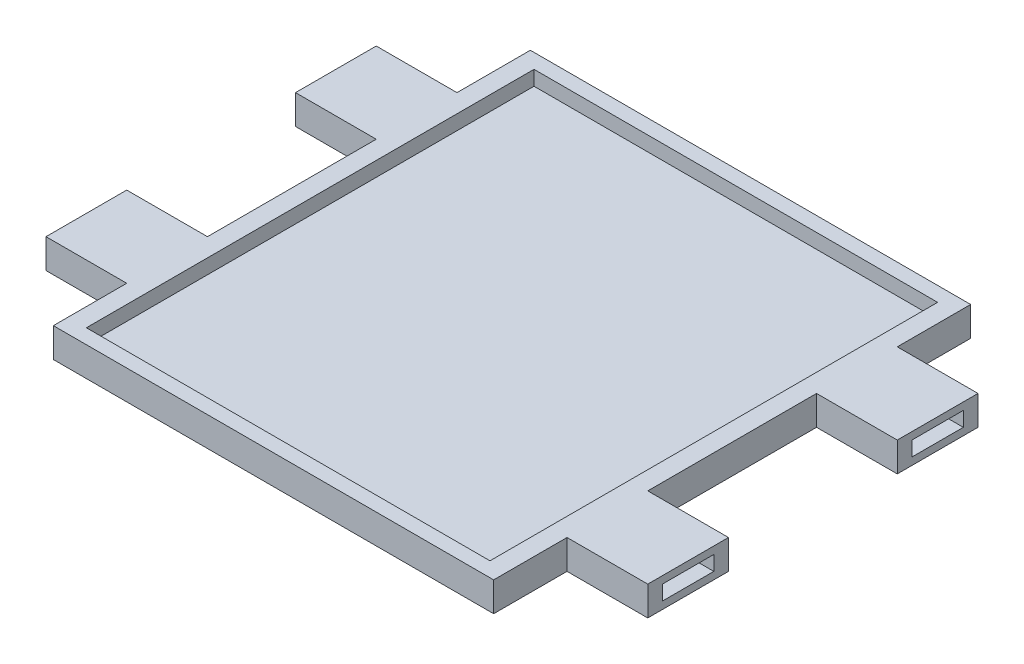
SolidWorks part; units mm, degrees
ref_plane "Alzado" through (0, 0, 0) normal (0, 0, 1) x (1, 0, 0)
ref_plane "Planta" through (0, 0, 0) normal (0, 1, 0) x (1, 0, 0)
ref_plane "Vista lateral" through (0, 0, 0) normal (1, 0, 0) x (0, 0, -1)
sketch "Croquis1" plane through (0, 0, 0) normal (0, 1, 0) x (1, 0, 0)
  line L0 (30, -32.5) -> (30, -22.5)
  line L1 (-30, 32.5) -> (30, 32.5)
  line L2 (30, -22.5) -> (30, -11.5) construction
  line L3 (-30, -32.5) -> (30, -32.5)
  line L4 (30, 11.5) -> (30, 22.5) construction
  line L5 (-30, 32.5) -> (30, -32.5) construction
  line L6 (-30, -32.5) -> (30, 32.5) construction
  line L7 (30, -22.5) -> (41, -22.5)
  line L8 (41, -22.5) -> (41, -11.5)
  line L9 (41, -11.5) -> (30, -11.5)
  line L10 (30, -11.5) -> (30, 11.5)
  line L11 (30, 11.5) -> (41, 11.5)
  line L12 (41, 11.5) -> (41, 22.5)
  line L13 (41, 22.5) -> (30, 22.5)
  line L14 (30, 22.5) -> (30, 32.5)
  line L15 (-30, 32.5) -> (-30, 22.5)
  line L16 (-30, 22.5) -> (-41, 22.5)
  line L17 (-41, 22.5) -> (-41, 11.5)
  line L18 (-41, 11.5) -> (-30, 11.5)
  line L19 (-30, 11.5) -> (-30, -11.5)
  line L20 (-30, -11.5) -> (-41, -11.5)
  line L21 (-41, -11.5) -> (-41, -22.5)
  line L22 (-41, -22.5) -> (-30, -22.5)
  line L23 (-30, -22.5) -> (-30, -32.5)
  line L24 (-30, 11.5) -> (-30, 22.5) construction
  line L25 (-30, -22.5) -> (-30, -11.5) construction
  point P0 (0, 0)
  dimension "D1" = 23
  dimension "D2" = 60
  dimension "D3" = 11
  dimension "D4" = 11
  dimension "D5" = 10
extrude "Saliente-Extruir1" add sketch "Croquis1" along normal blind 4
sketch "Croquis2" plane through (0, 4, 0) normal (0, 1, 0) x (1, 0, 0)
  line L0 (30, 32.5) -> (-30, 32.5) construction
  line L1 (-27.5, 30.5) -> (27.5, 30.5)
  line L2 (-27.5, 30.5) -> (-27.5, -30.5)
  line L3 (-27.5, -30.5) -> (27.5, -30.5)
  line L4 (27.5, 30.5) -> (27.5, -30.5)
  line L5 (-27.5, 30.5) -> (27.5, -30.5) construction
  line L6 (-27.5, -30.5) -> (27.5, 30.5) construction
  point P0 (0, 0)
  dimension "D1" = 2
  dimension "D2" = 55
extrude "Cortar-Extruir1" cut sketch "Croquis2" against normal blind 2
sketch "Croquis4" plane through (-41, 0, 0) normal (-1, 0, 0) x (0, 0, 1)
  line L0 (-22.5, 2) -> (-11.5, 2) construction
  line L2 (-20.5, 3) -> (-13.5, 3)
  line L3 (-20.5, 3) -> (-20.5, 1)
  line L4 (-20.5, 1) -> (-13.5, 1)
  line L5 (-22.5, 4) -> (-22.5, 0) construction
  line L6 (-11.5, 4) -> (-11.5, 0) construction
  line L7 (-17, 4) -> (-17, 0) construction
  line L8 (-22.5, 4) -> (-11.5, 4) construction
  line L9 (-22.5, 0) -> (-11.5, 0) construction
  line L10 (-13.5, 3) -> (-13.5, 1)
  line L11 (-20.5, 3) -> (-13.5, 1) construction
  line L12 (-20.5, 1) -> (-13.5, 3) construction
  point P0 (-17, 2)
  dimension "D1" = 7
  dimension "D2" = 2
extrude "Cortar-Extruir2" cut sketch "Croquis4" against normal blind 9
sketch "Croquis6" plane through (-41, 0, 0) normal (-1, 0, 0) x (0, 0, 1)
  line L0 (17, 4) -> (17, 0) construction
  line L1 (11.5, 4) -> (22.5, 4) construction
  line L2 (11.5, 0) -> (22.5, 0) construction
  line L4 (11.5, 4) -> (11.5, 0) construction
  line L5 (11.5, 2) -> (22.5, 2) construction
  line L6 (22.5, 4) -> (22.5, 0) construction
  line L7 (13.5, 3) -> (20.5, 3)
  line L8 (13.5, 3) -> (13.5, 1)
  line L9 (13.5, 1) -> (20.5, 1)
  line L10 (20.5, 3) -> (20.5, 1)
  line L11 (13.5, 3) -> (20.5, 1) construction
  line L12 (13.5, 1) -> (20.5, 3) construction
  point P6 (17, 2)
  dimension "D1" = 7
  dimension "D2" = 2
extrude "Cortar-Extruir3" cut sketch "Croquis6" against normal blind 9
sketch "Croquis7" plane through (41, 0, 0) normal (1, 0, 0) x (0, 0, -1)
  line L0 (-17, 0) -> (-17, 4) construction
  line L1 (-22.5, 0) -> (-11.5, 0) construction
  line L2 (-22.5, 4) -> (-11.5, 4) construction
  line L4 (-22.5, 4) -> (-22.5, 0) construction
  line L5 (-22.5, 2) -> (-11.5, 2) construction
  line L6 (-11.5, 4) -> (-11.5, 0) construction
  line L7 (-20.5, 1) -> (-13.5, 1)
  line L8 (-20.5, 1) -> (-20.5, 3)
  line L9 (-20.5, 3) -> (-13.5, 3)
  line L10 (-13.5, 1) -> (-13.5, 3)
  line L11 (-20.5, 1) -> (-13.5, 3) construction
  line L12 (-20.5, 3) -> (-13.5, 1) construction
  point P6 (-17, 2)
  dimension "D1" = 7
  dimension "D2" = 2
extrude "Cortar-Extruir4" cut sketch "Croquis7" against normal blind 9
sketch "Croquis8" plane through (41, 0, 0) normal (1, 0, 0) x (0, 0, -1)
  line L0 (17, 4) -> (17, 0) construction
  line L1 (11.5, 4) -> (22.5, 4) construction
  line L2 (11.5, 0) -> (22.5, 0) construction
  line L4 (11.5, 4) -> (11.5, 0) construction
  line L5 (11.5, 2) -> (22.5, 2) construction
  line L6 (22.5, 4) -> (22.5, 0) construction
  line L7 (13.5, 1) -> (20.5, 1)
  line L8 (13.5, 1) -> (13.5, 3)
  line L9 (13.5, 3) -> (20.5, 3)
  line L10 (20.5, 1) -> (20.5, 3)
  line L11 (13.5, 1) -> (20.5, 3) construction
  line L12 (13.5, 3) -> (20.5, 1) construction
  point P6 (17, 2)
  dimension "D1" = 7
  dimension "D2" = 2
extrude "Cortar-Extruir5" cut sketch "Croquis8" against normal blind 9
sketch "Croquis9" [suppressed] plane through (0, 0, 0) normal (0, 1, 0) x (1, 0, 0)
  line L0 (0, 0) -> (0, 50) construction
  line L1 (-105.9535, -48.7223) -> (-6.8702, -116.4165)
  line L2 (-105.9535, -48.7223) -> (6.8702, 116.4165)
  line L3 (6.8702, 116.4165) -> (105.9535, 48.7223)
  line L4 (-6.8702, -116.4165) -> (105.9535, 48.7223)
  line L5 (-105.9535, -48.7223) -> (105.9535, 48.7223) construction
  line L6 (6.8702, 116.4165) -> (-6.8702, -116.4165) construction
  point P0 (0, 0)
  point P6 (56.4118, 82.5694)
  dimension "D1" = 120
  dimension "D2" = 200
  dimension "D3" = 90
  dimension "D4" = 90
  dimension "D5" = 90
  dimension "D6" = 60
  dimension "D7" = 50
